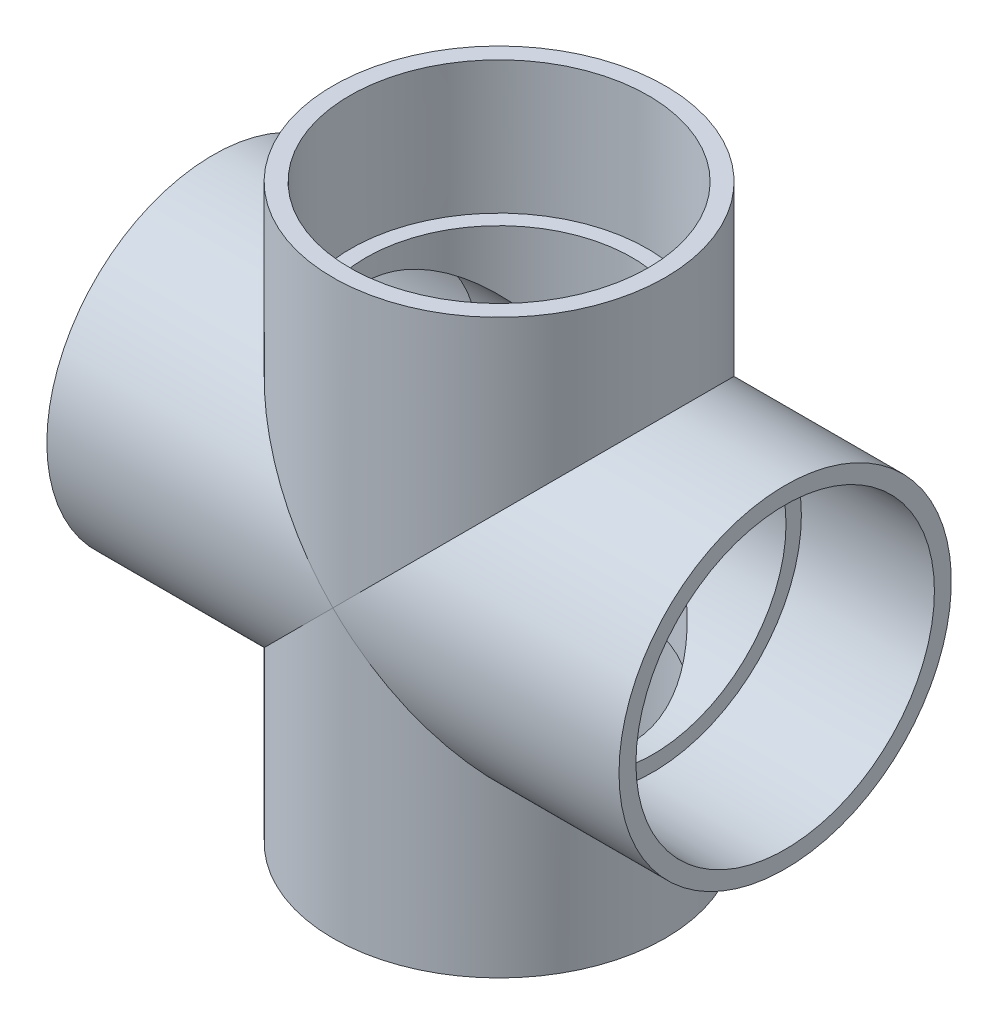
SolidWorks part; units mm, degrees
material "PVC Rigid"
ref_plane "Front Plane" through (0, 0, 0) normal (0, 0, 1) x (1, 0, 0)
ref_plane "Top Plane" through (0, 0, 0) normal (0, 1, 0) x (1, 0, 0)
ref_plane "Right Plane" through (0, 0, 0) normal (1, 0, 0) x (0, 0, -1)
sketch "Sketch0" plane through (0, 0, 0) normal (0, 0, 1) x (1, 0, 0)
  line L0 (-109.982, 0) -> (0, 0) construction
  line L1 (0, 0) -> (0, 109.982) construction
  line L2 (-59.182, 0) -> (0, 0) construction
  line L3 (0, 0) -> (0, 59.182) construction
  line L4 (-109.982, 63.881) -> (-109.982, -63.881) construction
  line L5 (-59.182, 57.0357) -> (-109.982, 57.3786) construction
  line L6 (-59.182, 57.0357) -> (-59.182, -57.0357) construction
  line L7 (-59.182, -57.0357) -> (-109.982, -57.3786) construction
  line L8 (-109.982, 57.3786) -> (-109.982, -57.3786) construction
  line L9 (-63.881, 109.982) -> (63.881, 109.982) construction
  line L10 (-57.3786, 109.982) -> (57.3786, 109.982) construction
  line L11 (57.3786, 109.982) -> (57.0357, 59.182) construction
  line L12 (57.0357, 59.182) -> (-57.0357, 59.182) construction
  line L13 (-57.0357, 59.182) -> (-57.3786, 109.982) construction
  line L14 (-59.182, 51.1302) -> (-59.182, -51.1302) construction
  line L15 (-109.982, 0) -> (-59.182, 0) construction
  line L16 (0, 109.982) -> (0, 59.182) construction
  line L17 (0, 0) -> (59.182, 0) construction
  line L18 (-51.1302, 59.182) -> (51.1302, 59.182) construction
  line L19 (59.182, 0) -> (109.982, 0) construction
  line L20 (0, 0) -> (0, -59.182) construction
  line L21 (0, -59.182) -> (0, -109.982) construction
  dimension "H" = 109.982
  dimension "G" = 59.182
  dimension "M" = 127.762
  dimension "OD A" = 114.7572
  dimension "OD B" = 114.0714
  dimension "ID" = 102.2604
sketch "Sketch1" plane through (0, 0, 0) normal (0, 0, 1) x (1, 0, 0)
  line L0 (-109.982, 0) -> (0, 0) construction
  line L1 (-109.982, 0) -> (0, 0) construction
  line L2 (0, 0) -> (0, -63.881) construction
  line L3 (-109.982, -63.881) -> (-59.182, -63.881)
  line L4 (-109.982, -63.881) -> (-109.982, -57.3786)
  line L5 (-109.982, -57.3786) -> (-59.182, -57.0357)
  line L6 (-59.182, -63.881) -> (-59.182, -57.0357)
  line L7 (-59.182, -63.881) -> (0, -63.881) construction
  line L8 (109.982, -57.3786) -> (59.182, -57.0357)
  line L9 (109.982, -63.881) -> (109.982, -57.3786)
  line L10 (59.182, -63.881) -> (59.182, -57.0357)
  line L11 (109.982, -63.881) -> (59.182, -63.881)
revolve "Revolve1" add sketch "Sketch1" angle 360 about L1
sketch "Sketch2" plane through (0, 0, 0) normal (0, 0, 1) x (1, 0, 0)
  line L0 (57.3786, 109.982) -> (57.0357, 59.182)
  line L1 (57.0357, 59.182) -> (63.881, 59.182)
  line L2 (63.881, 59.182) -> (63.881, 109.982)
  line L3 (63.881, 109.982) -> (57.3786, 109.982)
  line L4 (0, 0) -> (0, 109.982) construction
  line L5 (0, 0) -> (0, 109.982) construction
  line L6 (0, 0) -> (59.182, 0) construction
  line L7 (63.881, -109.982) -> (57.3786, -109.982)
  line L8 (63.881, -59.182) -> (63.881, -109.982)
  line L9 (57.0357, -59.182) -> (63.881, -59.182)
  line L10 (57.3786, -109.982) -> (57.0357, -59.182)
revolve "Revolve2" add sketch "Sketch2" angle 360 about L5
sketch "Sketch3" plane through (-59.182, 0, 0) normal (1, 0, 0) x (0, 0, -1)
  circle A0 centre (0, 0) radius 51.1302
  circle A1 centre (0, 0) radius 63.881
sketch "Sketch4" plane through (-59.182, 0, 0) normal (1, 0, 0) x (0, 0, -1)
  circle A0 centre (0, 0) radius 63.881 construction
  circle A1 centre (0, 0) radius 63.881
extrude "Boss-Extrude1" add sketch "Sketch4" along normal up to vertex
sketch "Sketch5" plane through (0, 59.182, 0) normal (0, -1, 0) x (1, 0, 0)
  circle A0 centre (0, 0) radius 63.881 construction
  circle A1 centre (0, 0) radius 63.881
  circle A2 centre (0, 0) radius 57.3786 construction
extrude "Boss-Extrude2" add sketch "Sketch5" along normal up to vertex
sketch "Sketch6" plane through (0, 0, 0) normal (0, 0, 1) x (1, 0, 0)
  line L0 (-109.982, -57.3786) -> (-59.182, -57.0357)
  line L1 (-59.182, -57.0357) -> (-59.182, -51.1302)
  line L2 (-59.182, -51.1302) -> (59.182, -51.1302)
  line L3 (59.182, -51.7184) -> (59.182, 51.7184) construction
  line L4 (0, -51.1302) -> (0, 0) construction
  line L5 (59.182, -57.0357) -> (59.182, -51.1302)
  line L6 (109.982, -57.3786) -> (109.982, 57.3786) construction
  line L7 (109.982, -63.881) -> (109.982, 63.881) construction
  line L8 (109.982, -57.3786) -> (109.982, 0)
  line L9 (109.982, 0) -> (-109.982, 0)
  line L10 (-109.982, 0) -> (-109.982, -57.3786)
  line L11 (109.982, -57.3786) -> (59.182, -57.0357)
revolve "Cut-Revolve1" cut sketch "Sketch6" angle 360 about L9
sketch "Sketch7" plane through (0, 0, 0) normal (0, 0, 1) x (1, 0, 0)
  line L0 (57.3786, 109.982) -> (57.0357, 59.182)
  line L1 (57.0357, 59.182) -> (51.1302, 59.182)
  line L2 (51.1302, 59.182) -> (51.1302, -59.182)
  line L4 (51.1302, 0) -> (0, 0) construction
  line L5 (0, 109.982) -> (0, -109.982)
  line L6 (-63.881, 109.982) -> (63.881, 109.982) construction
  line L7 (0, 109.982) -> (57.3786, 109.982)
  line L8 (57.0357, -59.182) -> (51.1302, -59.182)
  line L9 (57.3786, -109.982) -> (57.0357, -59.182)
  line L10 (0, 0) -> (59.182, 0) construction
  line L11 (0, -109.982) -> (57.3786, -109.982)
revolve "Cut-Revolve2" cut sketch "Sketch7" angle 360 about L5
